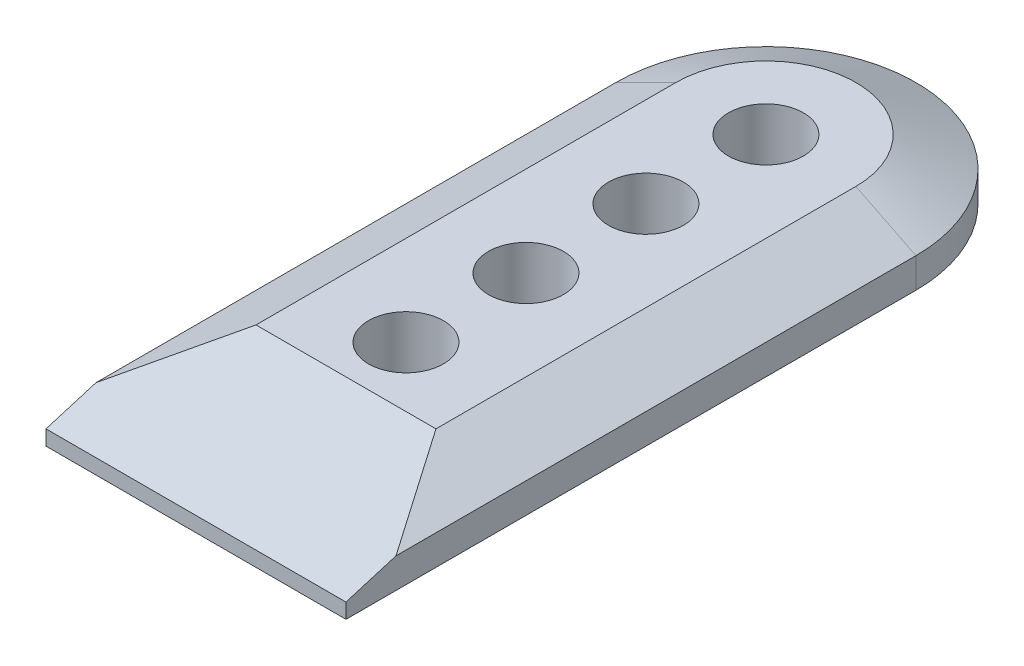
SolidWorks part; units mm, degrees
ref_plane "Front Plane" through (0, 0, 0) normal (0, 0, 1) x (1, 0, 0)
ref_plane "Top Plane" through (0, 0, 0) normal (0, 1, 0) x (1, 0, 0)
ref_plane "Right Plane" through (0, 0, 0) normal (1, 0, 0) x (0, 0, -1)
sketch "Sketch2" plane through (0, 0, 0) normal (0, 1, 0) x (1, 0, 0)
  line L0 (-31.75, 0) -> (31.75, 0)
  line L1 (31.75, 0) -> (31.75, 120.65)
  line L2 (-31.75, 0) -> (-31.75, 120.65)
  arc A0 (-31.75, 120.65) -> (31.75, 120.65) centre (0, 120.65) cw
  dimension "D1" = 31.75
  dimension "D2" = 120.65
extrude "Boss-Extrude1" add sketch "Sketch2" along normal blind 12.7
chamfer "Chamfer4" distance 6.35 distance2 12.7 3 edges at (31.75, 12.7, -60.325) (0, 12.7, -152.4) (-31.75, 12.7, -60.325)
chamfer "Chamfer5" distance 9.525 distance2 31.75 1 edges at (0, 12.7, 0)
sketch "Sketch5" plane through (0, 12.7, 0) normal (0, 1, 0) x (1, 0, 0)
  line L0 (0, 120.65) -> (0, 95.25) construction
  circle A0 centre (0, 120.65) radius 7.9375
  arc A1 (31.75, 120.65) -> (-31.75, 120.65) centre (0, 120.65) ccw construction
  circle A2 centre (0, 95.25) radius 7.9375
  circle A3 centre (0, 69.85) radius 7.9375
  circle A4 centre (0, 44.45) radius 7.9375
  point P5 (0, 152.4)
  dimension "D2" = 15.875
  dimension "D1" = 31.75
  dimension "D4" = 25.4
  dimension "D3" = 4
extrude "Cut-Extrude1" cut sketch "Sketch5" against normal through all
